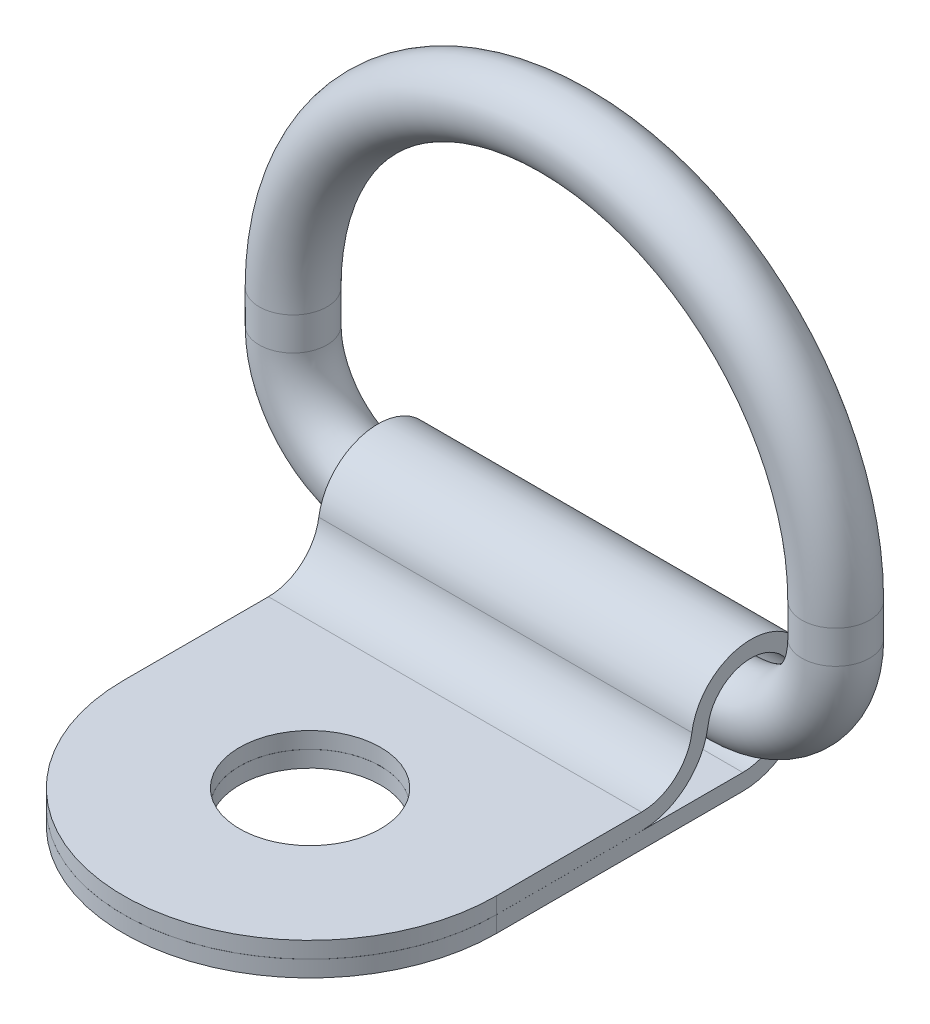
SolidWorks part; units mm, degrees
material "1023 Carbon Steel Sheet (SS)"
ref_plane "Front Plane" through (0, 0, 0) normal (0, 0, 1) x (1, 0, 0)
ref_plane "Top Plane" through (0, 0, 0) normal (0, 1, 0) x (1, 0, 0)
ref_plane "Right Plane" through (0, 0, 0) normal (1, 0, 0) x (0, 0, -1)
sketch "Sketch1" plane through (0, 0, 0) normal (0, 0, 1) x (1, 0, 0)
  line L0 (-7.8941, -1.5875) -> (7.8941, -1.5875) construction
  line L1 (0, 0) -> (0, 20.6375) construction
  line L2 (-14.2875, 6.35) -> (-14.2875, 4.8059) construction
  line L3 (-11.1125, 6.35) -> (-11.1125, 4.8059) construction
  line L4 (11.1125, 6.35) -> (11.1125, 4.8059) construction
  line L5 (14.2875, 6.35) -> (14.2875, 4.8059) construction
  line L6 (7.8941, 1.5875) -> (-7.8941, 1.5875) construction
  line L8 (0, 1.5875) -> (0, -1.5875) construction
  line L10 (-12.7, 6.35) -> (-12.7, 4.8059)
  line L11 (12.7, 6.35) -> (12.7, 4.8059)
  line L12 (-7.8941, 0) -> (7.8941, 0)
  arc A0 (14.2875, 6.35) -> (-14.2875, 6.35) centre (0, 6.35) ccw construction
  arc A1 (11.1125, 6.35) -> (-11.1125, 6.35) centre (0, 6.35) ccw construction
  circle A2 centre (0, 19.05) radius 1.5875 construction
  circle A3 centre (0, 0) radius 1.5875 construction
  arc A4 (12.7, 6.35) -> (-12.7, 6.35) centre (0, 6.35) ccw
  arc A5 (-7.8941, 0) -> (-12.7, 4.8059) centre (-7.8941, 4.8059) cw
  arc A6 (7.8941, 0) -> (12.7, 4.8059) centre (7.8941, 4.8059) ccw
  arc A7 (-7.8941, 1.5875) -> (-11.1125, 4.8059) centre (-7.8941, 4.8059) cw construction
  arc A8 (-7.8941, -1.5875) -> (-14.2875, 4.8059) centre (-7.8941, 4.8059) cw construction
  arc A9 (7.8941, -1.5875) -> (14.2875, 4.8059) centre (7.8941, 4.8059) ccw construction
  arc A10 (7.8941, 1.5875) -> (11.1125, 4.8059) centre (7.8941, 4.8059) ccw construction
  dimension "C" = 3.175
  dimension "A" = 22.225
  dimension "B" = 22.225
sketch "Sketch2" plane through (0, 0, 0) normal (1, 0, 0) x (0, 0, -1)
  circle A0 centre (0, 0) radius 1.5875
sweep "Sweep1" add profiles "Sketch2" path "Sketch1"
sketch "Sketch3" plane through (0, 0, 0) normal (1, 0, 0) x (0, 0, -1)
  line L0 (-20.6375, -3.175) -> (-0.381, -3.175)
  line L1 (-20.6375, -3.175) -> (-20.6375, -2.413)
  line L2 (-20.6375, -2.413) -> (-0.381, -2.413)
  line L4 (-20.6375, -2.4105) -> (-20.6375, -1.6485)
  line L5 (-20.6375, -1.6485) -> (-5.1231, -1.6485)
  line L6 (-20.6375, -2.4105) -> (-5.1231, -2.4105)
  line L7 (-11.9062, -3.175) -> (-11.9062, -2.413) construction
  circle A0 centre (0, 0) radius 2.032 construction
  arc A1 (-2.7658, 0.3956) -> (2.794, 0) centre (0, 0) cw
  arc A2 (-2.7658, 0.3956) -> (-5.1231, -1.6485) centre (-5.1231, 0.7328) cw
  arc A3 (-5.1231, -2.4105) -> (-2.0115, 0.2877) centre (-5.1231, 0.7328) ccw
  arc A4 (-2.0115, 0.2877) -> (2.032, 0) centre (0, 0) cw
  arc A5 (-0.381, -2.413) -> (2.032, 0) centre (-0.381, 0) ccw
  arc A6 (-0.381, -3.175) -> (2.794, 0) centre (-0.381, 0) ccw
  dimension "D1" = 4.064
  dimension "D6" = 2.3813
  dimension "D2" = 0.762
  dimension "D3" = 3.175
  dimension "D4" = 20.6375
  dimension "D7" = 0.0025
  dimension "D8" = 11.9062
extrude "Boss-Extrude1" add sketch "Sketch3" along normal mid plane 17.4625 separate body
sketch "Sketch4" plane through (0, -3.175, 0) normal (0, -1, 0) x (1, 0, 0)
  line L0 (-8.7312, 11.9062) -> (-8.7312, 20.6375)
  line L1 (-8.7312, 20.6375) -> (-8.7312, 21.9075)
  line L2 (-8.7312, 21.9075) -> (8.7313, 21.9075)
  line L3 (8.7313, 21.9075) -> (8.7312, 20.6375)
  line L4 (8.7312, 20.6375) -> (8.7312, 11.9062)
  line L5 (8.7312, 20.6375) -> (-8.7312, 20.6375) construction
  line L6 (8.7312, 5.1231) -> (8.7312, 20.6375) construction
  arc A0 (8.7312, 11.9062) -> (-8.7312, 11.9062) centre (0, 11.9062) ccw
  circle A1 centre (0, 11.9062) radius 3.302
  dimension "D3" = 6.604
  dimension "D2" = 1.27
extrude "Cut-Extrude1" cut sketch "Sketch4" against normal through all
